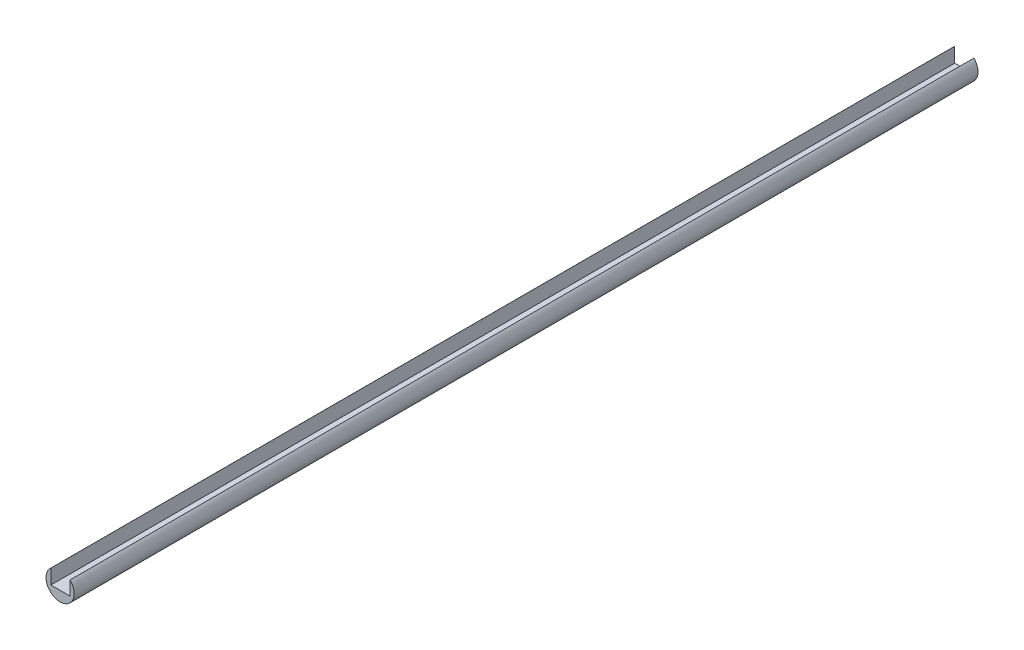
SolidWorks part; units mm, degrees
ref_plane "Front Plane" through (0, 0, 0) normal (0, 0, 1) x (1, 0, 0)
ref_plane "Top Plane" through (0, 0, 0) normal (0, 1, 0) x (1, 0, 0)
ref_plane "Right Plane" through (0, 0, 0) normal (1, 0, 0) x (0, 0, -1)
sketch "Sketch1" plane through (0, 0, 0) normal (0, 0, 1) x (1, 0, 0)
  circle A0 centre (-85.8143, -49.5449) radius 9.3435 construction
  circle A1 centre (-85.8143, -49.5449) radius 9.3435
extrude "Boss-Extrude1" add sketch "Sketch1" along normal blind 600
sketch "Sketch2" plane through (0, 0, 600) normal (0, 0, 1) x (1, 0, 0)
  line L0 (-91.9221, -42.4742) -> (-91.9221, -52.234)
  line L1 (-91.9221, -52.234) -> (-79.199, -52.234)
  line L2 (-79.199, -52.234) -> (-79.199, -42.9465)
  line L3 (-85.5606, -52.234) -> (-85.5606, -40.2049) construction
  circle A0 centre (-85.8143, -49.5449) radius 9.3435 construction
  arc A2 (-79.199, -42.9465) -> (-91.9221, -42.4742) centre (-85.8143, -49.5449) ccw
extrude "Cut-Extrude1" cut sketch "Sketch2" against normal through all
